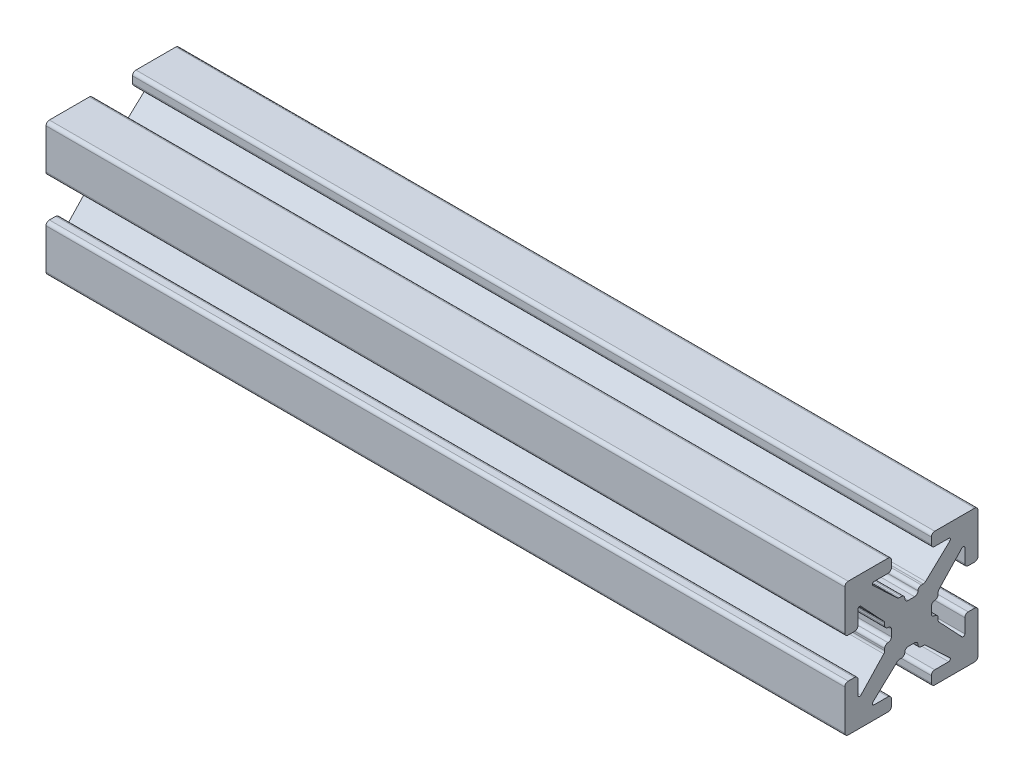
SolidWorks part; units mm, degrees
ref_plane "Front Plane" through (0, 0, 0) normal (0, 0, 1) x (1, 0, 0)
ref_plane "Top Plane" through (0, 0, 0) normal (0, 1, 0) x (1, 0, 0)
ref_plane "Right Plane" through (0, 0, 0) normal (1, 0, 0) x (0, 0, -1)
sketch "Sketch1" plane through (0, 0, 0) normal (1, 0, 0) x (0, 0, -1)
  line L0 (0, 0) -> (0, 1.4986) construction
  line L1 (-0.2413, 1.4986) -> (0.2413, 1.4986)
  line L2 (5.0038, 1.7526) -> (5.0038, 4.7498)
  line L3 (0.7493, 2.0066) -> (0.8899, 2.0066)
  line L4 (1.0639, 2.0756) -> (2.8908, 3.7937)
  line L5 (2.8038, 4.0132) -> (1.7526, 4.0132)
  line L6 (1.4986, 4.2672) -> (1.4986, 4.7498)
  line L7 (1.7526, 5.0038) -> (4.7498, 5.0038)
  line L8 (5.0038, 5.0038) -> (0, 0) construction
  line L9 (0, 0) -> (8.6271, 0) construction
  line L10 (0, 0) -> (0, 5.0038) construction
  line L11 (4.2672, 1.4986) -> (4.7498, 1.4986)
  line L12 (4.0132, 2.8038) -> (4.0132, 1.7526)
  line L13 (2.0756, 1.0639) -> (3.7937, 2.8908)
  line L14 (2.0066, 0.7493) -> (2.0066, 0.8899)
  line L15 (1.4986, -0.2413) -> (1.4986, 0.2413)
  line L16 (0, 0) -> (1.4986, 0) construction
  line L17 (-0.2413, -1.4986) -> (0.2413, -1.4986)
  line L18 (0.7493, -2.0066) -> (0.8899, -2.0066)
  line L19 (1.0639, -2.0756) -> (2.8908, -3.7937)
  line L20 (2.8038, -4.0132) -> (1.7526, -4.0132)
  line L21 (1.4986, -4.2672) -> (1.4986, -4.7498)
  line L22 (1.7526, -5.0038) -> (4.7498, -5.0038)
  line L23 (5.0038, -1.7526) -> (5.0038, -4.7498)
  line L24 (4.2672, -1.4986) -> (4.7498, -1.4986)
  line L25 (4.0132, -2.8038) -> (4.0132, -1.7526)
  line L26 (2.0756, -1.0639) -> (3.7937, -2.8908)
  line L27 (2.0066, -0.7493) -> (2.0066, -0.8899)
  line L28 (-0.7493, 2.0066) -> (-0.8899, 2.0066)
  line L29 (-1.0639, 2.0756) -> (-2.8908, 3.7937)
  line L30 (-2.8038, 4.0132) -> (-1.7526, 4.0132)
  line L31 (-1.4986, 4.2672) -> (-1.4986, 4.7498)
  line L32 (-1.7526, 5.0038) -> (-4.7498, 5.0038)
  line L33 (-5.0038, 1.7526) -> (-5.0038, 4.7498)
  line L34 (-4.2672, 1.4986) -> (-4.7498, 1.4986)
  line L35 (-4.0132, 2.8038) -> (-4.0132, 1.7526)
  line L36 (-2.0756, 1.0639) -> (-3.7937, 2.8908)
  line L37 (-2.0066, 0.7493) -> (-2.0066, 0.8899)
  line L38 (-1.4986, -0.2413) -> (-1.4986, 0.2413)
  line L39 (-2.0066, -0.7493) -> (-2.0066, -0.8899)
  line L40 (-2.0756, -1.0639) -> (-3.7937, -2.8908)
  line L41 (-4.0132, -2.8038) -> (-4.0132, -1.7526)
  line L42 (-4.2672, -1.4986) -> (-4.7498, -1.4986)
  line L43 (-5.0038, -1.7526) -> (-5.0038, -4.7498)
  line L44 (-1.7526, -5.0038) -> (-4.7498, -5.0038)
  line L45 (-1.4986, -4.2672) -> (-1.4986, -4.7498)
  line L46 (-2.8038, -4.0132) -> (-1.7526, -4.0132)
  line L47 (-1.0639, -2.0756) -> (-2.8908, -3.7937)
  line L48 (-0.7493, -2.0066) -> (-0.8899, -2.0066)
  arc A0 (2.8908, 3.7937) -> (2.8038, 4.0132) centre (2.8038, 3.8862) ccw
  arc A1 (0.4953, 1.7526) -> (0.7493, 2.0066) centre (0.7493, 1.7526) cw
  arc A2 (0.8899, 2.0066) -> (1.0639, 2.0756) centre (0.8899, 2.2606) ccw
  arc A3 (1.7526, 4.0132) -> (1.4986, 4.2672) centre (1.7526, 4.2672) cw
  arc A4 (1.4986, 4.7498) -> (1.7526, 5.0038) centre (1.7526, 4.7498) cw
  arc A5 (0.2413, 1.4986) -> (0.4953, 1.7526) centre (0.2413, 1.7526) ccw
  arc A6 (4.7498, 1.4986) -> (5.0038, 1.7526) centre (4.7498, 1.7526) ccw
  arc A7 (4.0132, 1.7526) -> (4.2672, 1.4986) centre (4.2672, 1.7526) ccw
  arc A8 (3.7937, 2.8908) -> (4.0132, 2.8038) centre (3.8862, 2.8038) cw
  arc A9 (2.0066, 0.8899) -> (2.0756, 1.0639) centre (2.2606, 0.8899) cw
  arc A10 (1.7526, 0.4953) -> (2.0066, 0.7493) centre (1.7526, 0.7493) ccw
  arc A11 (1.4986, 0.2413) -> (1.7526, 0.4953) centre (1.7526, 0.2413) cw
  arc A12 (0.2413, -1.4986) -> (0.4953, -1.7526) centre (0.2413, -1.7526) cw
  arc A13 (0.4953, -1.7526) -> (0.7493, -2.0066) centre (0.7493, -1.7526) ccw
  arc A14 (0.8899, -2.0066) -> (1.0639, -2.0756) centre (0.8899, -2.2606) cw
  arc A15 (2.8908, -3.7937) -> (2.8038, -4.0132) centre (2.8038, -3.8862) cw
  arc A16 (1.7526, -4.0132) -> (1.4986, -4.2672) centre (1.7526, -4.2672) ccw
  arc A17 (1.4986, -4.7498) -> (1.7526, -5.0038) centre (1.7526, -4.7498) ccw
  arc A18 (4.7498, -1.4986) -> (5.0038, -1.7526) centre (4.7498, -1.7526) cw
  arc A19 (4.0132, -1.7526) -> (4.2672, -1.4986) centre (4.2672, -1.7526) cw
  arc A20 (3.7937, -2.8908) -> (4.0132, -2.8038) centre (3.8862, -2.8038) ccw
  arc A21 (2.0066, -0.8899) -> (2.0756, -1.0639) centre (2.2606, -0.8899) ccw
  arc A22 (1.7526, -0.4953) -> (2.0066, -0.7493) centre (1.7526, -0.7493) cw
  arc A23 (1.4986, -0.2413) -> (1.7526, -0.4953) centre (1.7526, -0.2413) ccw
  arc A24 (-0.2413, 1.4986) -> (-0.4953, 1.7526) centre (-0.2413, 1.7526) cw
  arc A25 (-0.4953, 1.7526) -> (-0.7493, 2.0066) centre (-0.7493, 1.7526) ccw
  arc A26 (-0.8899, 2.0066) -> (-1.0639, 2.0756) centre (-0.8899, 2.2606) cw
  arc A27 (-2.8908, 3.7937) -> (-2.8038, 4.0132) centre (-2.8038, 3.8862) cw
  arc A28 (-1.7526, 4.0132) -> (-1.4986, 4.2672) centre (-1.7526, 4.2672) ccw
  arc A29 (-1.4986, 4.7498) -> (-1.7526, 5.0038) centre (-1.7526, 4.7498) ccw
  arc A30 (-4.7498, 1.4986) -> (-5.0038, 1.7526) centre (-4.7498, 1.7526) cw
  arc A31 (-4.0132, 1.7526) -> (-4.2672, 1.4986) centre (-4.2672, 1.7526) cw
  arc A32 (-3.7937, 2.8908) -> (-4.0132, 2.8038) centre (-3.8862, 2.8038) ccw
  arc A33 (-2.0066, 0.8899) -> (-2.0756, 1.0639) centre (-2.2606, 0.8899) ccw
  arc A34 (-1.7526, 0.4953) -> (-2.0066, 0.7493) centre (-1.7526, 0.7493) cw
  arc A35 (-1.4986, 0.2413) -> (-1.7526, 0.4953) centre (-1.7526, 0.2413) ccw
  arc A36 (-1.4986, -0.2413) -> (-1.7526, -0.4953) centre (-1.7526, -0.2413) cw
  arc A37 (-1.7526, -0.4953) -> (-2.0066, -0.7493) centre (-1.7526, -0.7493) ccw
  arc A38 (-2.0066, -0.8899) -> (-2.0756, -1.0639) centre (-2.2606, -0.8899) cw
  arc A39 (-3.7937, -2.8908) -> (-4.0132, -2.8038) centre (-3.8862, -2.8038) cw
  arc A40 (-4.0132, -1.7526) -> (-4.2672, -1.4986) centre (-4.2672, -1.7526) ccw
  arc A41 (-4.7498, -1.4986) -> (-5.0038, -1.7526) centre (-4.7498, -1.7526) ccw
  arc A42 (-1.4986, -4.7498) -> (-1.7526, -5.0038) centre (-1.7526, -4.7498) cw
  arc A43 (-1.7526, -4.0132) -> (-1.4986, -4.2672) centre (-1.7526, -4.2672) cw
  arc A44 (-2.8908, -3.7937) -> (-2.8038, -4.0132) centre (-2.8038, -3.8862) ccw
  arc A45 (-0.8899, -2.0066) -> (-1.0639, -2.0756) centre (-0.8899, -2.2606) ccw
  arc A46 (-0.4953, -1.7526) -> (-0.7493, -2.0066) centre (-0.7493, -1.7526) cw
  arc A47 (-0.2413, -1.4986) -> (-0.4953, -1.7526) centre (-0.2413, -1.7526) ccw
  arc A48 (-4.7498, 5.0038) -> (-5.0038, 4.7498) centre (-4.7498, 4.7498) ccw
  arc A49 (-5.0038, -4.7498) -> (-4.7498, -5.0038) centre (-4.7498, -4.7498) ccw
  arc A50 (4.7498, -5.0038) -> (5.0038, -4.7498) centre (4.7498, -4.7498) ccw
  arc A51 (4.7498, 5.0038) -> (5.0038, 4.7498) centre (4.7498, 4.7498) cw
  point P14 (3.1242, 4.0132)
  point P19 (0.9906, 2.0066)
  point P150 (0, -1.4986)
  point P152 (-5.0038, 5.0038)
  point P155 (-5.0038, -5.0038)
  point P158 (5.0038, -5.0038)
  dimension "D10" = 0.127
  dimension "D11" = 0.254
  dimension "D2" = 0.254
  dimension "D1" = 10.0076
  dimension "D3" = 2.9972
  dimension "D4" = 0.508
  dimension "D5" = 2.9972
  dimension "D6" = 0.9906
  dimension "D7" = 1.6256
  dimension "D8" = 1.9812
  dimension "D9" = 0.9906
extrude "Boss.-Extru.1" add sketch "Sketch1" along normal blind 60
